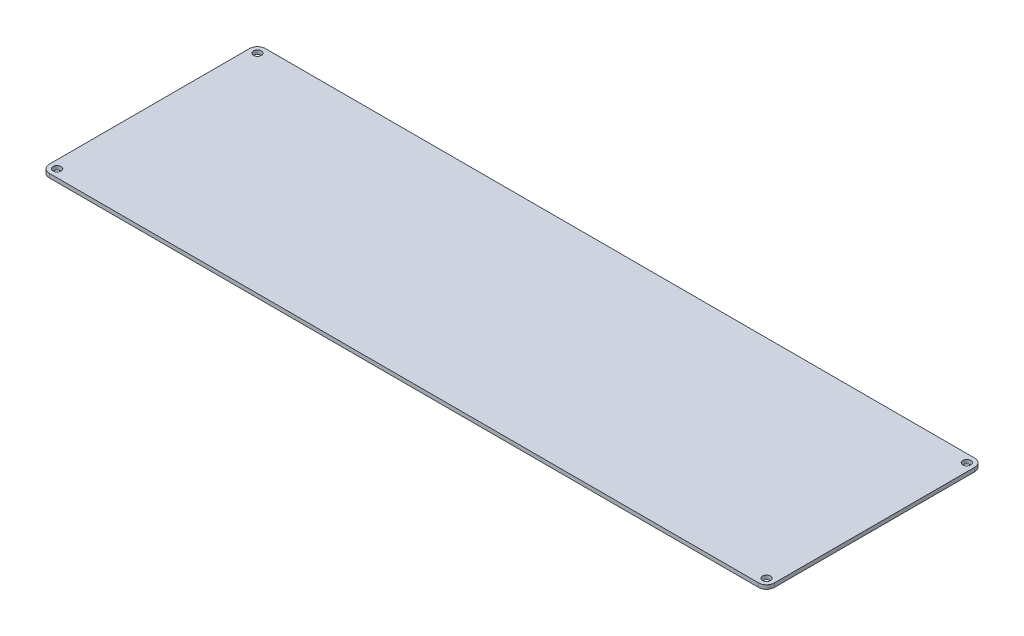
SolidWorks part; units mm, degrees
material "Delrin 2700 NC010, Low Viscosity Acetal Copolymer (SS)"
ref_plane "Front" through (0, 0, 0) normal (0, 0, 1) x (1, 0, 0)
ref_plane "Top" through (0, 0, 0) normal (0, 1, 0) x (1, 0, 0)
ref_plane "Right" through (0, 0, 0) normal (1, 0, 0) x (0, 0, -1)
sketch "Sketch1" plane through (0, 0, 0) normal (0, 1, 0) x (1, 0, 0)
  line L0 (13.7815, 113.4471) -> (20.1315, 113.4471) construction
  line L5 (-25.0185, 167.2471) -> (13.7815, 167.2471) construction
  line L6 (-25.0185, 167.2471) -> (-25.0185, 113.4471) construction
  line L7 (-25.0185, 113.4471) -> (13.7815, 113.4471) construction
  line L8 (13.7815, 167.2471) -> (13.7815, 113.4471) construction
  line L9 (-131.3685, 167.2471) -> (-31.3685, 167.2471) construction
  line L10 (-131.3685, 167.2471) -> (-131.3685, 77.2471) construction
  line L11 (-131.3685, 77.2471) -> (-31.3685, 77.2471) construction
  line L12 (-31.3685, 167.2471) -> (-31.3685, 77.2471) construction
  line L13 (20.1315, 167.2471) -> (58.9315, 167.2471) construction
  line L14 (20.1315, 167.2471) -> (20.1315, 113.4471) construction
  line L15 (20.1315, 113.4471) -> (58.9315, 113.4471) construction
  line L16 (58.9315, 167.2471) -> (58.9315, 113.4471) construction
  line L17 (65.2815, 167.2471) -> (104.0815, 167.2471) construction
  line L18 (65.2815, 167.2471) -> (65.2815, 113.4471) construction
  line L19 (65.2815, 113.4471) -> (104.0815, 113.4471) construction
  line L20 (104.0815, 167.2471) -> (104.0815, 113.4471) construction
  line L21 (58.9315, 113.4471) -> (65.2815, 113.4471) construction
  line L22 (-241.8585, 192.6471) -> (327.6015, 192.6471) construction
  line L27 (-248.2085, 198.9971) -> (333.9515, 198.9971)
  line L28 (-248.2085, 198.9971) -> (-248.2085, 25.5151)
  line L29 (-248.2085, 25.5151) -> (333.9515, 25.5151)
  line L30 (333.9515, 198.9971) -> (333.9515, 25.5151)
  line L31 (327.6015, 192.6471) -> (327.6015, 31.8651) construction
  line L32 (-241.8585, 31.8651) -> (327.6015, 31.8651) construction
  line L33 (-241.8585, 192.6471) -> (-241.8585, 31.8651) construction
  line L34 (-25.0185, 167.2471) -> (-31.3685, 167.2471) construction
  line L35 (104.0815, 167.2471) -> (110.4315, 167.2471) construction
  line L36 (110.4315, 167.2471) -> (308.5515, 167.2471) construction
  line L37 (110.4315, 167.2471) -> (110.4315, 57.2651) construction
  line L38 (110.4315, 57.2651) -> (308.5515, 57.2651) construction
  line L39 (308.5515, 167.2471) -> (308.5515, 57.2651) construction
  line L40 (-222.8085, 167.2471) -> (-222.8085, 124.0671) construction
  circle A0 centre (-241.8585, 192.6471) radius 3.175
  circle A1 centre (-241.8585, 31.8651) radius 3.175
  circle A2 centre (327.6015, 31.8651) radius 3.175
  circle A3 centre (327.6015, 192.6471) radius 3.175
  dimension "D14" = 6.35
  dimension "D2" = 25.4
  dimension "D3" = 38.8
  dimension "D4" = 100
  dimension "D5" = 90
  dimension "D6" = 53.8
  dimension "D7" = 25.4
  dimension "D8" = 25.4
  dimension "D9" = 198.12
  dimension "D10" = 6.35
  dimension "D11" = 19.05
  dimension "D12" = 109.982
  dimension "D13" = 6.35
extrude "Boss-Extrude1" add sketch "Sketch1" against normal blind 3.175 contours L30 L27 L28 L29 A3 A2 A1 A0
fillet "Fillet1" radius 6.35 4 edges at (-248.2085, -1.5875, -198.9971) (-248.2085, -1.5875, -25.5151) (333.9515, -1.5875, -25.5151) (333.9515, -1.5875, -198.9971)
